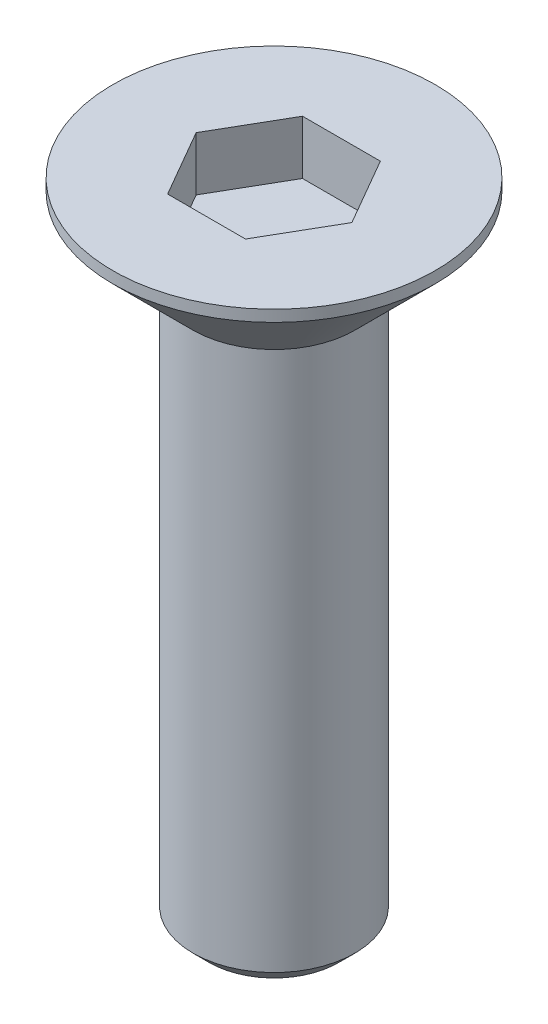
SolidWorks part; units mm, degrees
material "acero"
ref_plane "Alzado" through (0, 0, 0) normal (0, 0, 1) x (1, 0, 0)
ref_plane "Planta" through (0, 0, 0) normal (0, 1, 0) x (1, 0, 0)
ref_plane "Vista lateral" through (0, 0, 0) normal (1, 0, 0) x (0, 0, -1)
sketch "Croquis1" plane through (0, 0, 0) normal (0, 0, 1) x (1, 0, 0)
  line L0 (0, 0) -> (0, -60.9498) construction
  line L1 (0, 0) -> (3.2, 0)
  line L2 (1.5, -1.7) -> (3.2, 0)
  line L4 (1.5, -1.7) -> (1.5, -12)
  line L5 (1.5, -12) -> (0, -12)
  line L6 (0, -12) -> (0, 0)
  dimension "D1" = 12
  dimension "D2" = 45
  dimension "D3" = 1.7
  dimension "D4" = 3
revolve "Revolución1" add sketch "Croquis1" angle 360 about L0
chamfer "Chaflán2" distance 0.3 angle 45 1 edges at (0, 0, 3.2)
chamfer "Chaflán3" distance 0.3 angle 45 1 edges at (0, -12, 1.5)
sketch "Croquis3" plane through (0, 0, 0) normal (0, 1, 0) x (1, 0, 0)
  line L1 (-0.7217, 1.25) -> (-1.4434, 0)
  line L2 (-1.4434, 0) -> (-0.7217, -1.25)
  line L3 (-0.7217, -1.25) -> (0.7217, -1.25)
  line L4 (0.7217, -1.25) -> (1.4434, 0)
  line L5 (1.4434, 0) -> (0.7217, 1.25)
  line L6 (0.7217, 1.25) -> (-0.7217, 1.25)
  circle A0 centre (0, 0) radius 1.25 construction
  dimension "D1" = 2.5
extrude "Cortar-Extruir2" cut sketch "Croquis3" against normal blind 1
